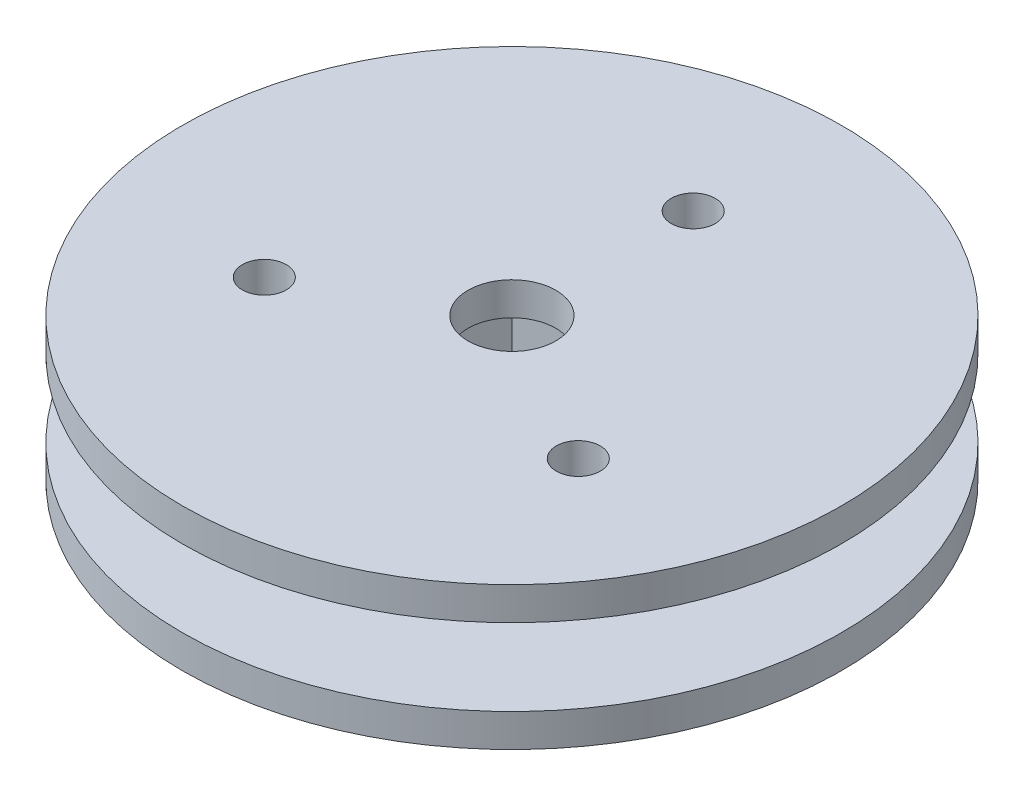
SolidWorks part; units mm, degrees
ref_plane "前视基准面" through (0, 0, 0) normal (0, 0, 1) x (1, 0, 0)
ref_plane "上视基准面" through (0, 0, 0) normal (0, 1, 0) x (1, 0, 0)
ref_plane "右视基准面" through (0, 0, 0) normal (1, 0, 0) x (0, 0, -1)
sketch "草图1" plane through (0, 0, 0) normal (0, 1, 0) x (1, 0, 0)
  circle A0 centre (0, 0) radius 15
  dimension "D1" = 30
extrude "凸台-拉伸1" add sketch "草图1" along normal blind 1.5
sketch "草图2" plane through (0, 1.5, 0) normal (0, 1, 0) x (1, 0, 0)
  line L0 (0, 15) -> (0, -15) construction
  line L1 (-15, 0) -> (15, 0) construction
  line L3 (-3.75, 3.75) -> (3.75, 3.75)
  line L4 (-3.75, 3.75) -> (-3.75, -3.75)
  line L5 (-3.75, -3.75) -> (3.75, -3.75)
  line L6 (3.75, 3.75) -> (3.75, -3.75)
  circle A0 centre (0, 0) radius 15 construction
  circle A1 centre (0, 0) radius 6
  dimension "D5" = 12
  dimension "D1" = 7.5
  dimension "D2" = 7.5
  dimension "D3" = 3.75
  dimension "D4" = 3.75
extrude "凸台-拉伸2" add sketch "草图2" along normal blind 3.5 contours A1 | L4 L3 L6 L5
sketch "草图3" plane through (0, 1.5, 0) normal (0, 1, 0) x (1, 0, 0)
  line L1 (-3.75, 3.75) -> (3.75, 3.75)
  line L2 (-3.75, 3.75) -> (-3.75, -3.75)
  line L3 (-3.75, -3.75) -> (3.75, -3.75)
  line L4 (3.75, 3.75) -> (3.75, -3.75)
extrude "切除-拉伸1" cut sketch "草图3" against normal blind 3.5
sketch "草图4" plane through (0, 5, 0) normal (0, 1, 0) x (1, 0, 0)
  circle A0 centre (0, 0) radius 15
  dimension "D1" = 30
extrude "凸台-拉伸3" add sketch "草图4" along normal blind 1.5
sketch "草图5" plane through (0, 6.5, 0) normal (0, 1, 0) x (1, 0, 0)
  line L0 (0, 15) -> (0, -15) construction
  line L1 (-15, 0) -> (15, 0) construction
  circle A0 centre (0, 0) radius 15 construction
  circle A1 centre (0, 0) radius 2
  dimension "D1" = 4
extrude "切除-拉伸2" cut sketch "草图5" against normal blind 1.5
sketch "草图6" plane through (0, 6.5, 0) normal (0, 1, 0) x (1, 0, 0)
  line L0 (0, 15) -> (0, 0) construction
  line L1 (0, 0) -> (-12.9904, -7.5) construction
  line L2 (0, 0) -> (12.9904, -7.5) construction
  circle A0 centre (0, 0) radius 15 construction
  circle A1 centre (0, 0) radius 6 construction
  circle A2 centre (0, 8.25) radius 1
  circle A3 centre (-7.1447, -4.125) radius 1
  circle A4 centre (7.1447, -4.125) radius 1
  circle A5 centre (0, 0) radius 8.25 construction
  dimension "D3" = 12
  dimension "D4" = 16.5
  dimension "D5" = 2
  dimension "D6" = 2
  dimension "D7" = 2
  dimension "D1" = 120
  dimension "D2" = 120
extrude "切除-拉伸3" cut sketch "草图6" against normal blind 10
